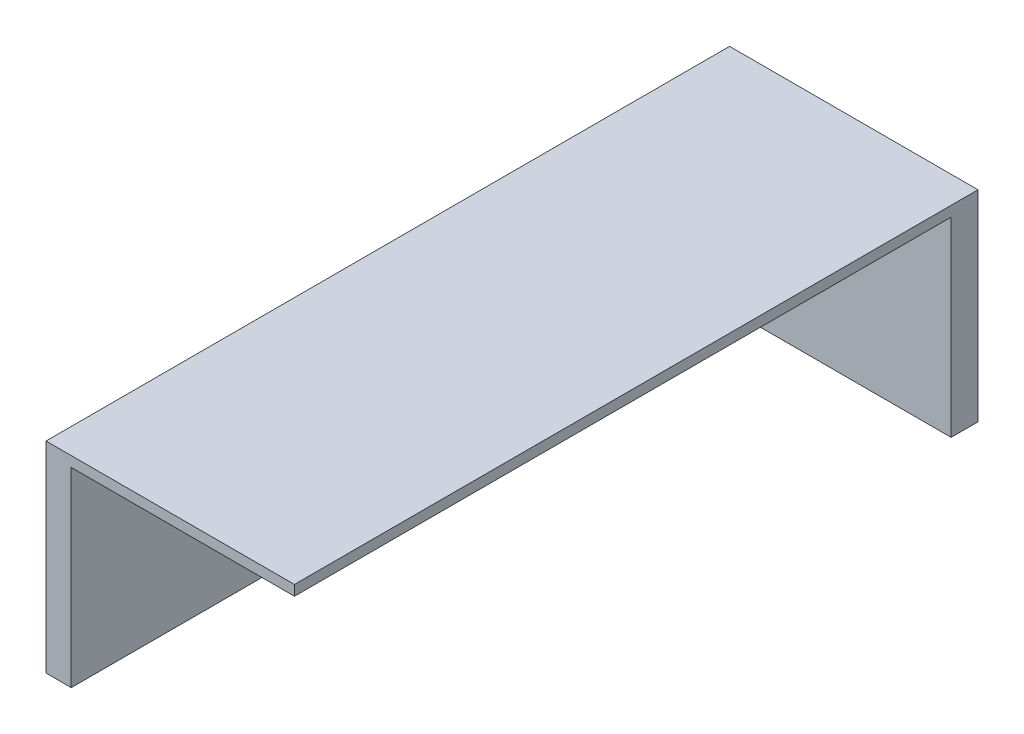
SolidWorks part; units mm, degrees
ref_plane "Front Plane" through (0, 0, 0) normal (0, 0, 1) x (1, 0, 0)
ref_plane "Top Plane" through (0, 0, 0) normal (0, 1, 0) x (1, 0, 0)
ref_plane "Right Plane" through (0, 0, 0) normal (1, 0, 0) x (0, 0, -1)
sketch "Sketch1" plane through (0, 0, 0) normal (0, 1, 0) x (1, 0, 0)
  circle A0 centre (0, 0) radius 28.1
extrude "Boss-Extrude1" add sketch "Sketch1" along normal blind 1
sketch "Sketch2" plane through (0, 1, 0) normal (0, 1, 0) x (1, 0, 0)
  circle A0 centre (0, -7) radius 18.6
extrude "Cut-Extrude1" cut sketch "Sketch2" against normal blind 58.8
sketch "Sketch3" plane through (0, 0, 0) normal (0, -1, 0) x (-1, 0, 0)
  line L1 (111.3415, -182.1414) -> (-111.3415, -182.1414)
  line L2 (111.3415, -182.1414) -> (111.3415, 182.1414)
  line L3 (111.3415, 182.1414) -> (-111.3415, 182.1414)
  line L4 (-111.3415, -182.1414) -> (-111.3415, 182.1414)
  line L5 (111.3415, -182.1414) -> (-111.3415, 182.1414) construction
  line L6 (111.3415, 182.1414) -> (-111.3415, -182.1414) construction
  point P0 (0, 0)
extrude "Boss-Extrude2" add sketch "Sketch3" along normal blind 58.8
sketch "Sketch4" plane through (0, -58.8, 0) normal (0, -1, 0) x (-1, 0, 0)
  line L1 (103.9587, -174.2721) -> (-103.9587, -174.2721)
  line L2 (103.9587, -174.2721) -> (103.9587, 174.2721)
  line L3 (103.9587, 174.2721) -> (-103.9587, 174.2721)
  line L4 (-103.9587, -174.2721) -> (-103.9587, 174.2721)
  line L5 (103.9587, -174.2721) -> (-103.9587, 174.2721) construction
  line L6 (103.9587, 174.2721) -> (-103.9587, -174.2721) construction
  point P0 (0, 0)
extrude "Cut-Extrude2" cut sketch "Sketch4" against normal blind 55.8
sketch "Sketch6" plane through (0, 1, 0) normal (0, 1, 0) x (1, 0, 0)
  circle A1 centre (0, 18.75) radius 3.75
sketch "Sketch9" plane through (0, 0, 0) normal (0, 1, 0) x (1, 0, 0)
  circle A1 centre (0, -7) radius 3
extrude "Cut-Extrude8" cut sketch "Sketch9" against normal blind 10
sketch "Sketch10" plane through (0, 1, 0) normal (0, 1, 0) x (1, 0, 0)
  circle A2 centre (0, 19.85) radius 3.75
extrude "Cut-Extrude9" cut sketch "Sketch10" against normal blind 10
sketch "Sketch11" plane through (0, -58.8, 0) normal (0, -1, 0) x (-1, 0, 0)
  line L23 (38.6585, -17.8586) -> (111.3415, -17.8586)
  line L24 (38.6585, -17.8586) -> (38.6585, 182.1414)
  line L25 (111.3415, 182.1414) -> (-111.3415, 182.1414) construction
  line L26 (38.6585, 182.1414) -> (-111.3415, 182.1414)
  line L27 (-111.3415, 182.1414) -> (-111.3415, -182.1414)
  line L30 (-111.3415, -182.1414) -> (111.3415, -182.1414)
  line L31 (111.3415, -182.1414) -> (111.3415, -17.8586)
extrude "Cut-Extrude12" cut sketch "Sketch11" against normal blind 500
extrude "Cut-Extrude5" cut sketch "Sketch6" against normal blind 400
sketch "Sketch8" plane through (0, 0, -182.1414) normal (0, 0, -1) x (-1, 0, 0)
  circle A0 centre (-86.5737, -25.0112) radius 10
extrude "Cut-Extrude7" cut sketch "Sketch8" against normal blind 10 contours A0
